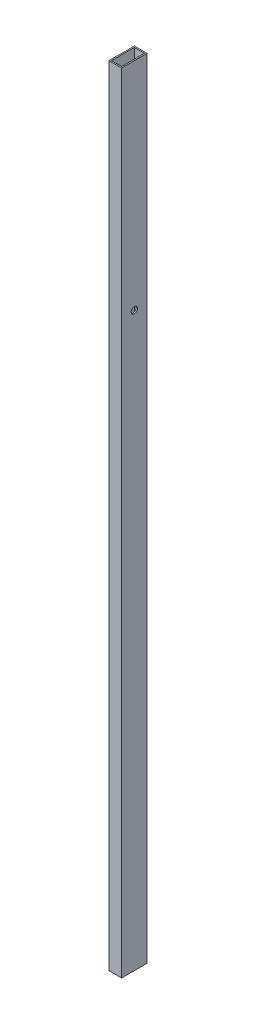
SolidWorks part; units mm, degrees
ref_plane "Спереди" through (0, 0, 0) normal (0, 0, 1) x (1, 0, 0)
ref_plane "Сверху" through (0, 0, 0) normal (0, 1, 0) x (1, 0, 0)
ref_plane "Справа" through (0, 0, 0) normal (1, 0, 0) x (0, 0, -1)
sketch "Эскиз1" plane through (0, 0, 0) normal (0, 1, 0) x (1, 0, 0)
  line L1 (-10, 20) -> (10, 20)
  line L2 (-10, 20) -> (-10, -20)
  line L3 (-10, -20) -> (10, -20)
  line L4 (10, 20) -> (10, -20)
  line L5 (-10, 20) -> (10, -20) construction
  line L6 (-10, -20) -> (10, 20) construction
  point P0 (0, 0)
extrude "Вытянуть-Тонкостенный1" add sketch "Эскиз1" along normal blind 1240 thin
sketch "Эскиз2" plane through (10, 0, 0) normal (1, 0, 0) x (0, 0, -1)
  circle A0 centre (0, 900) radius 5
extrude "Вырез-Вытянуть1" cut sketch "Эскиз2" against normal through all
sketch "Эскиз3" plane through (-10, 0, 0) normal (-1, 0, 0) x (0, 0, 1)
  circle A0 centre (0, 720) radius 5
  circle A1 centre (0, 580) radius 5
  circle A2 centre (0, 440) radius 5
  dimension "D1" = 3
extrude "Вырез-Вытянуть2" cut sketch "Эскиз3" against normal blind 10
